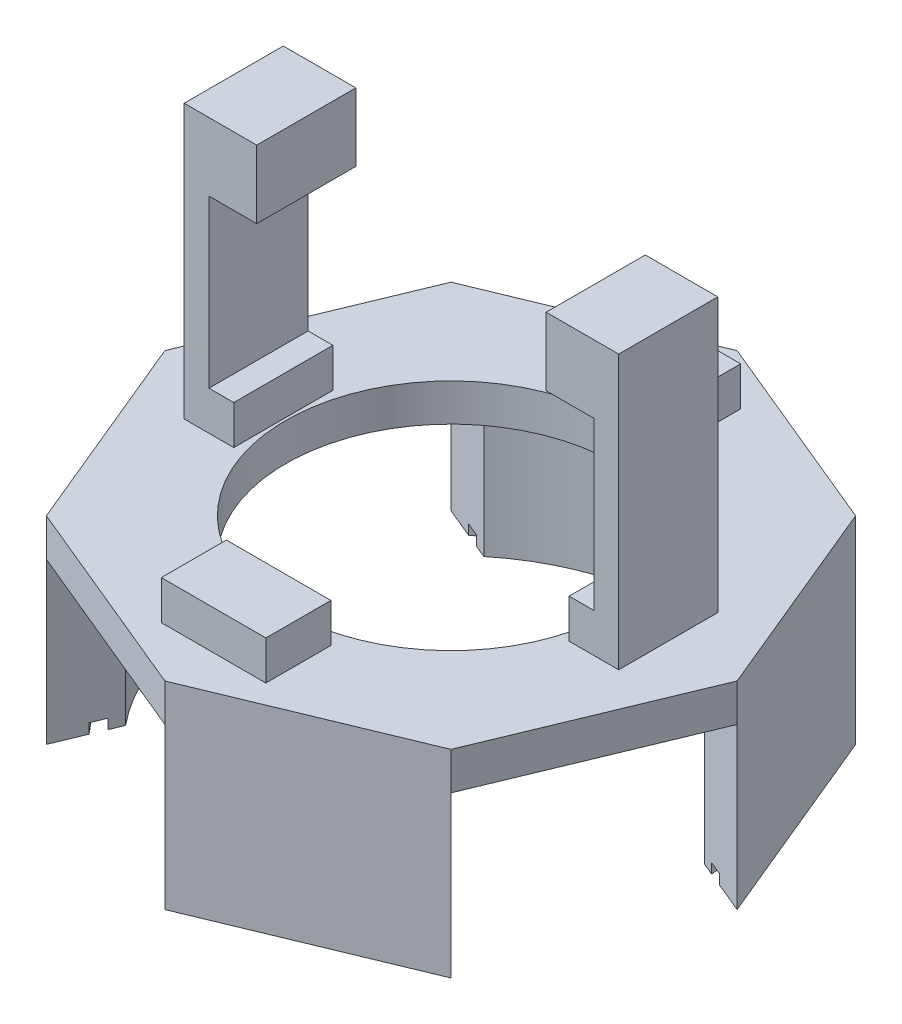
SolidWorks part; units mm, degrees
ref_plane "Front Plane" through (0, 0, 0) normal (0, 0, 1) x (1, 0, 0)
ref_plane "Top Plane" through (0, 0, 0) normal (0, 1, 0) x (1, 0, 0)
ref_plane "Right Plane" through (0, 0, 0) normal (1, 0, 0) x (0, 0, -1)
sketch "Sketch1" plane through (0, 0, 0) normal (0, 1, 0) x (1, 0, 0)
  line L0 (-154.639, 0) -> (154.639, 0) construction
  line L3 (-55, 0) -> (55, 0) construction
  line L4 (0, -167.8871) -> (0, 167.8871) construction
  line L6 (21.9942, 0) -> (15.5523, 15.5523)
  line L7 (15.5523, 15.5523) -> (0, 21.9942)
  line L8 (0, 21.9942) -> (-15.5523, 15.5523)
  line L9 (-15.5523, 15.5523) -> (-21.9942, 0)
  line L10 (-21.9942, 0) -> (-15.5523, -15.5523)
  line L11 (-15.5523, -15.5523) -> (0, -21.9942)
  line L12 (0, -21.9942) -> (15.5523, -15.5523)
  line L13 (15.5523, -15.5523) -> (21.9942, 0)
  circle A0 centre (0, 0) radius 20.32 construction
  point P4 (0, 0)
  point P11 (0, 0)
  dimension "D1" = 40.64
extrude "Boss-Extrude1" add sketch "Sketch1" against normal mid plane 15.22
sketch "Sketch5" plane through (0, -7.61, 0) normal (0, -1, 0) x (1, 0, 0)
  line L0 (-36.8608, 0) -> (36.8608, 0) construction
  line L2 (55, 0) -> (-55, 0) construction
  line L3 (0, -31.5933) -> (0, 31.5933) construction
  line L4 (0, -55) -> (0, 55) construction
  circle A0 centre (0, 0) radius 17.78
  point P4 (0, 0)
  point P12 (0, 0)
extrude "Cut-Extrude2" cut sketch "Sketch5" against normal blind 12.3444
sketch "Sketch6" plane through (0, 4.7344, 0) normal (0, -1, 0) x (1, 0, 0)
  line L0 (-35.4865, 0) -> (35.4865, 0) construction
  line L2 (55, 0) -> (-55, 0) construction
  line L3 (0, -29.7556) -> (0, 29.7556) construction
  circle A0 centre (0, 0) radius 12.7
  point P5 (0, 0)
  point P11 (0, 0)
extrude "Cut-Extrude3" cut sketch "Sketch6" against normal through all
sketch "Sketch7" plane through (-7.7761, 0, 18.7732) normal (-0.3827, 0, 0.9239) x (0.9239, 0, 0.3827)
  line L0 (-8.4168, 4.7144) -> (8.4168, 4.7144)
  line L1 (-8.4168, -7.61) -> (-8.4168, 7.61) construction
  line L2 (8.4168, -7.61) -> (8.4168, 7.61) construction
  line L3 (-8.4168, 7.61) -> (8.4168, 7.61) construction
  line L4 (-8.4168, 4.7144) -> (-8.4168, -7.61)
  line L5 (-8.4168, -7.61) -> (8.4168, -7.61)
  line L6 (8.4168, -7.61) -> (8.4168, 4.7144)
  dimension "D1" = 2.8956
extrude "Cut-Extrude4" cut sketch "Sketch7" against normal through all
sketch "Sketch8" plane through (18.7732, 0, 7.7761) normal (0.9239, 0, 0.3827) x (0.3827, 0, -0.9239)
  line L0 (-8.4168, 4.7144) -> (8.4168, 4.7144)
  line L1 (-8.4168, -7.61) -> (-8.4168, 7.61) construction
  line L2 (8.4168, -7.61) -> (8.4168, 7.61) construction
  line L3 (-8.4168, 7.61) -> (8.4168, 7.61) construction
  line L4 (-8.4168, 4.7144) -> (-8.4168, -7.61)
  line L5 (-8.4168, -7.61) -> (8.4168, -7.61)
  line L6 (8.4168, -7.61) -> (8.4168, 4.7144)
  dimension "D1" = 2.8956
extrude "Cut-Extrude5" cut sketch "Sketch8" against normal through all
sketch "Sketch10" plane through (0, -7.61, 0) normal (0, -1, 0) x (1, 0, 0)
  line L0 (-36.0387, 0) -> (36.0387, 0) construction
  line L2 (0, -24.8848) -> (0, 24.8848) construction
  line L3 (0, -55) -> (0, 55) construction
  line L4 (55, 0) -> (-55, 0) construction
  circle A0 centre (0, 0) radius 19.6953
  circle A1 centre (0, 0) radius 18.7036
  point P8 (0, 0)
  point P14 (0, 0)
  point P15 (0, 0)
extrude "Cut-Extrude7" cut sketch "Sketch10" against normal blind 0.762 contours A0 | A1
sketch "Sketch11" plane through (0, 7.61, 0) normal (0, 1, 0) x (1, 0, 0)
  line L0 (0, -23.5109) -> (0, 23.5109) construction
  line L1 (16.7005, -3.81) -> (12.8905, -3.81)
  line L2 (0, -55) -> (0, 55) construction
  line L3 (-42.6851, 0) -> (42.6851, 0) construction
  line L4 (-55, 0) -> (55, 0) construction
  line L5 (-16.7005, 3.81) -> (-12.8905, 3.81)
  line L6 (-16.7005, 3.81) -> (-16.7005, -3.81)
  line L7 (-16.7005, -3.81) -> (-12.8905, -3.81)
  line L8 (-12.8905, 3.81) -> (-12.8905, -3.81)
  line L9 (-16.7005, 3.81) -> (-12.8905, -3.81) construction
  line L10 (-16.7005, -3.81) -> (-12.8905, 3.81) construction
  line L11 (16.7005, -3.81) -> (12.8905, 3.81) construction
  line L12 (16.7005, 3.81) -> (12.8905, -3.81) construction
  line L13 (12.8905, 3.81) -> (12.8905, -3.81)
  line L14 (16.7005, 3.81) -> (12.8905, 3.81)
  line L15 (16.7005, 3.81) -> (16.7005, -3.81)
  point P0 (-14.7955, 0)
  point P4 (0, 0)
  point P12 (0, 0)
extrude "Boss-Extrude2" add sketch "Sketch11" along normal blind 21.02
sketch "Sketch13" plane through (0, 28.63, 0) normal (0, 1, 0) x (1, 0, 0)
  line L0 (0, -24.8068) -> (0, 24.8068) construction
  line L2 (0, -55) -> (0, 55) construction
  line L3 (-24.8991, 0) -> (24.8991, 0) construction
  line L4 (-55, 0) -> (55, 0) construction
  line L6 (-14.7955, 3.81) -> (14.7955, 3.81)
  line L7 (-14.7955, 3.81) -> (-14.7955, -3.81)
  line L8 (-14.7955, -3.81) -> (14.7955, -3.81)
  line L9 (14.7955, 3.81) -> (14.7955, -3.81)
  line L10 (-14.7955, 3.81) -> (14.7955, -3.81) construction
  line L11 (-14.7955, -3.81) -> (14.7955, 3.81) construction
  point P0 (0, 0)
  point P4 (0, 0)
  point P12 (0, 0)
  dimension "D1" = 29.591
extrude "Cut-Extrude8" cut sketch "Sketch13" against normal blind 18.02
sketch "Sketch15" plane through (0, 7.61, 0) normal (0, 1, 0) x (1, 0, 0)
  line L0 (-27.1165, 0) -> (27.1165, 0) construction
  line L2 (-55, 0) -> (55, 0) construction
  line L3 (0, -24.622) -> (0, 24.622) construction
  line L4 (0, -55) -> (0, 55) construction
  line L5 (-4.019, -13.25) -> (4.019, -13.25)
  line L6 (-4.019, 18.25) -> (4.019, 18.25)
  line L7 (-4.019, 18.25) -> (-4.019, 13.25)
  line L8 (-4.019, 13.25) -> (4.019, 13.25)
  line L9 (4.019, 18.25) -> (4.019, 13.25)
  line L10 (-4.019, 18.25) -> (4.019, 13.25) construction
  line L11 (-4.019, 13.25) -> (4.019, 18.25) construction
  line L12 (4.019, -18.25) -> (4.019, -13.25)
  line L13 (-4.019, -18.25) -> (4.019, -18.25)
  line L14 (-4.019, -18.25) -> (-4.019, -13.25)
  line L15 (-4.019, -13.25) -> (4.019, -18.25) construction
  line L16 (-4.019, -18.25) -> (4.019, -13.25) construction
  point P0 (0, 15.75)
  point P3 (-4.019, -15.75)
  point P4 (0, 0)
  point P12 (0, 0)
  point P21 (0, -15.75)
  point P22 (-4.019, 15.75)
  dimension "D1" = 31.5
extrude "Boss-Extrude3" add sketch "Sketch15" along normal blind 3
sketch "Sketch16" plane through (-14.7955, 0, 0) normal (1, 0, 0) x (0, 0, -1)
  line L0 (3.81, 10.61) -> (3.81, 28.63) construction
  line L1 (-3.81, 28.63) -> (3.81, 28.63)
  line L2 (-3.81, 28.63) -> (-3.81, 23.4)
  line L3 (-3.81, 23.4) -> (3.81, 23.4)
  line L4 (3.81, 28.63) -> (3.81, 23.4)
  dimension "D1" = 5.23
extrude "Boss-Extrude4" add sketch "Sketch16" along normal blind 3.67
mirror "Mirror1" about plane through (0, 0, 0) normal (1, 0, 0) of "Boss-Extrude4"
